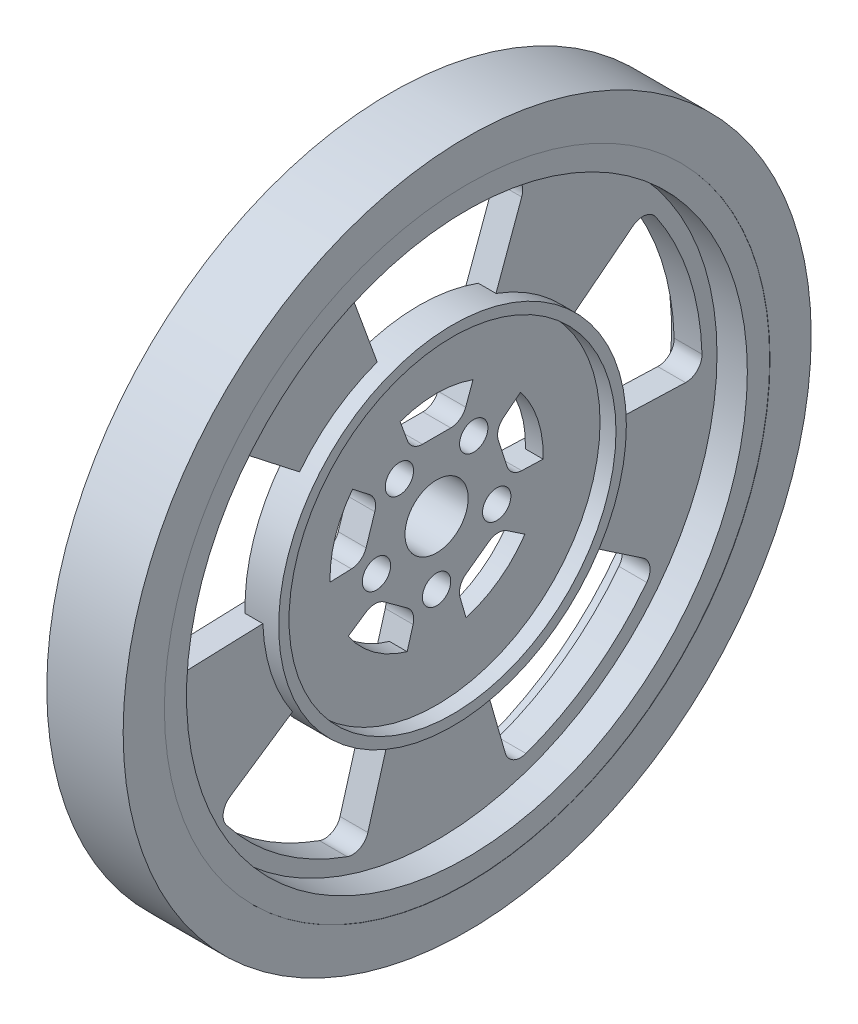
SolidWorks part; units mm, degrees
ref_plane "Front Plane" through (0, 0, 0) normal (0, 0, 1) x (1, 0, 0)
ref_plane "Top Plane" through (0, 0, 0) normal (0, 1, 0) x (1, 0, 0)
ref_plane "Right Plane" through (0, 0, 0) normal (1, 0, 0) x (0, 0, -1)
sketch "Sketch1" plane through (0, 0, 0) normal (1, 0, 0) x (0, 0, -1)
  circle A0 centre (0, 0) radius 34.544
  dimension "D1" = 69.088
extrude "Boss-Extrude1" add sketch "Sketch1" along normal blind 7.62
sketch "Sketch2" plane through (7.62, 0, 0) normal (1, 0, 0) x (0, 0, -1)
  circle A0 centre (0, 0) radius 28.1686
  dimension "D1" = 56.3372
extrude "Cut-Extrude1" cut sketch "Sketch2" against normal blind 3.048
sketch "Sketch3" plane through (0, 0, 0) normal (-1, 0, 0) x (0, 0, 1)
  circle A0 centre (0, 0) radius 28.1686
  circle A1 centre (0, 0) radius 4.3688
  dimension "D1" = 56.3372
  dimension "D2" = 8.7376
extrude "Cut-Extrude2" cut sketch "Sketch3" against normal blind 1.778
sketch "Sketch4" plane through (1.778, 0, 0) normal (-1, 0, 0) x (0, 0, 1)
  line L0 (0, 0) -> (0, 34.544) construction
  line L1 (-2.54, 6.985) -> (2.54, 6.985)
  line L2 (2.54, 6.985) -> (9.1143, 25.0643)
  line L3 (-9.1143, 25.0643) -> (-2.54, 6.985)
  circle A0 centre (0, 0) radius 34.544 construction
  arc A1 (9.1143, 25.0643) -> (-9.1143, 25.0643) centre (0, 0) ccw
  circle A2 centre (0, 0) radius 28.1686 construction
  dimension "D3" = 26.67
  dimension "D1" = 5.08
  dimension "D2" = 6.985
extrude "Cut-Extrude3" cut sketch "Sketch4" against normal through all
fillet "Fillet1" radius 1.6002 4 edges at (3.175, 25.0643, 9.1143) (3.175, 25.0643, -9.1143) (3.175, 6.985, 2.54) (3.175, 6.985, -2.54)
pattern_circular "CirPattern1" count 5 over 360 about axis through (0, 0, 0) along (1, 0, 0) of "Fillet1", "Cut-Extrude3"
sketch "Sketch5" plane through (4.572, 0, 0) normal (1, 0, 0) x (0, 0, -1)
  circle A0 centre (0, 0) radius 17.4625
  circle A1 centre (0, 0) radius 10.7061
  dimension "D1" = 34.925
  dimension "D2" = 21.4122
extrude "Boss-Extrude2" add sketch "Sketch5" against normal blind 1.778
sketch "Sketch6" plane through (4.572, 0, 0) normal (1, 0, 0) x (0, 0, -1)
  circle A0 centre (0, 0) radius 17.4625
  circle A1 centre (0, 0) radius 16.4211
  dimension "D1" = 34.925
  dimension "D2" = 1.0414
extrude "Boss-Extrude4" add sketch "Sketch6" along normal blind 1.6002
sketch "Sketch7" plane through (4.572, 0, 0) normal (1, 0, 0) x (0, 0, -1)
  circle A0 centre (0, 0) radius 3.175
  dimension "D1" = 6.35
extrude "Cut-Extrude4" cut sketch "Sketch7" against normal through all
sketch "Sketch8" plane through (4.572, 0, 0) normal (1, 0, 0) x (0, 0, -1)
  circle A0 centre (0, -6.35) radius 1.4224
  dimension "D1" = 2.8448
  dimension "D2" = 6.35
extrude "Cut-Extrude5" cut sketch "Sketch8" against normal through all
pattern_circular "CirPattern2" count 5 over 360 about axis through (0, 0, 0) along (1, 0, 0) of "Cut-Extrude5"
sketch "Sketch9" plane through (7.62, 0, 0) normal (1, 0, 0) x (0, 0, -1)
  circle A0 centre (0, 0) radius 34.5567
  circle A1 centre (0, 0) radius 30.4165
  dimension "D1" = 69.1134
  dimension "D2" = 60.833
extrude "Boss-Extrude5" add sketch "Sketch9" along normal blind 0.0254 and the other way blind 7.6454
